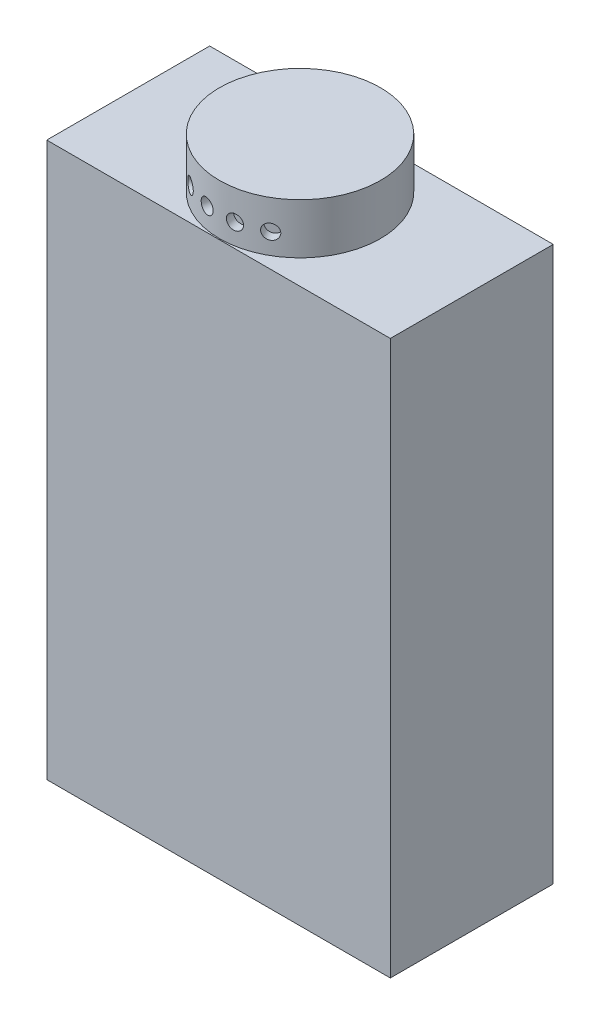
SolidWorks part; units mm, degrees
ref_plane "Front Plane" through (0, 0, 0) normal (0, 0, 1) x (1, 0, 0)
ref_plane "Top Plane" through (0, 0, 0) normal (0, 1, 0) x (1, 0, 0)
ref_plane "Right Plane" through (0, 0, 0) normal (1, 0, 0) x (0, 0, -1)
sketch "Sketch1" plane through (0, 0, 0) normal (0, 1, 0) x (1, 0, 0)
  line L1 (-58, 27.5) -> (58, 27.5)
  line L2 (-58, 27.5) -> (-58, -27.5)
  line L3 (-58, -27.5) -> (58, -27.5)
  line L4 (58, 27.5) -> (58, -27.5)
  line L5 (-58, 27.5) -> (58, -27.5) construction
  line L6 (-58, -27.5) -> (58, 27.5) construction
  point P0 (0, 0)
  dimension "D1" = 116
  dimension "D2" = 55
extrude "Boss-Extrude1" add sketch "Sketch1" along normal blind 187
sketch "Sketch2" plane through (0, 187, 0) normal (0, 1, 0) x (1, 0, 0)
  circle A0 centre (0, 0) radius 27.164
extrude "Boss-Extrude2" add sketch "Sketch2" along normal blind 17
ref_plane "Plane1" through (0, 194, 0) normal (0, 1, 0) x (-1, 0, 0)
sketch "Sketch4" plane through (0, 194, 0) normal (0, 1, 0) x (-1, 0, 0)
  line L0 (0, 35.8537) -> (0, 0) construction
  line L1 (0, 0) -> (-23.2435, 40.2589) construction
  line L2 (-14.5828, 25.2581) -> (-12.4177, 26.5081)
  line L3 (-12.4177, 26.5081) -> (-9.8618, 22.0812)
  line L4 (-9.8618, 22.0812) -> (-12.0269, 20.8312)
  line L5 (-14.5828, 25.2581) -> (-12.0269, 20.8312)
  dimension "D1" = 30
  dimension "D2" = 2.5
revolve "Cut-Revolve1" cut sketch "Sketch4" angle 360 about L1
pattern_circular "CirPattern1" count 4 over 60 about axis through (0, 0, 0) along (0, 1, 0) of "Cut-Revolve1"
